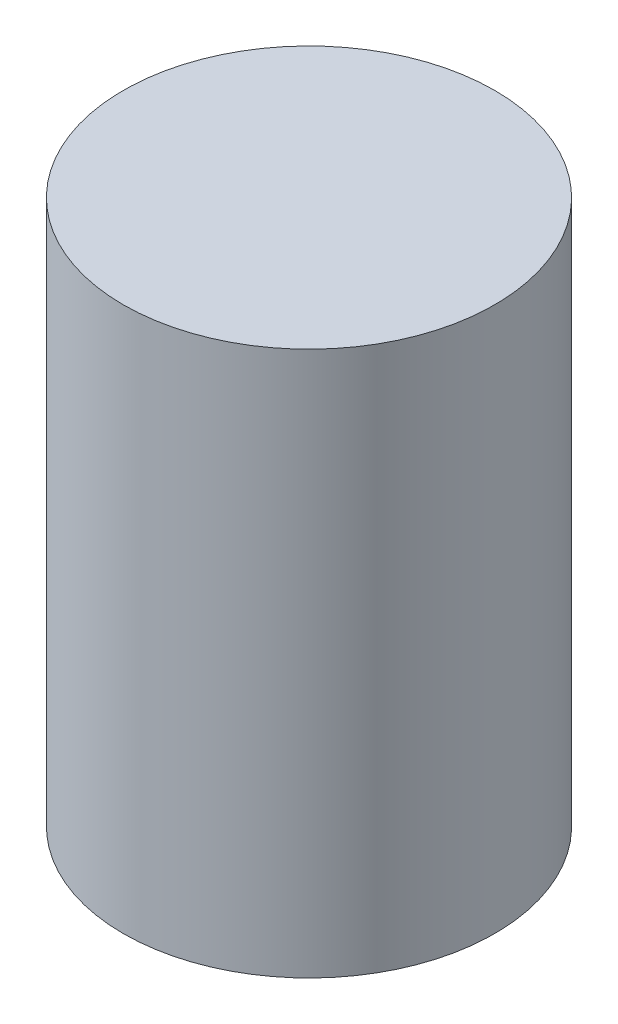
SolidWorks part; units mm, degrees
ref_plane "Front Plane" through (0, 0, 0) normal (0, 0, 1) x (1, 0, 0)
ref_plane "Top Plane" through (0, 0, 0) normal (0, 1, 0) x (1, 0, 0)
ref_plane "Right Plane" through (0, 0, 0) normal (1, 0, 0) x (0, 0, -1)
sketch "Sketch1" plane through (0, 0, 0) normal (0, 1, 0) x (1, 0, 0)
  circle A0 centre (-15.3208, 23.227) radius 11
extrude "Boss-Extrude1" add sketch "Sketch1" along normal blind 32.26
